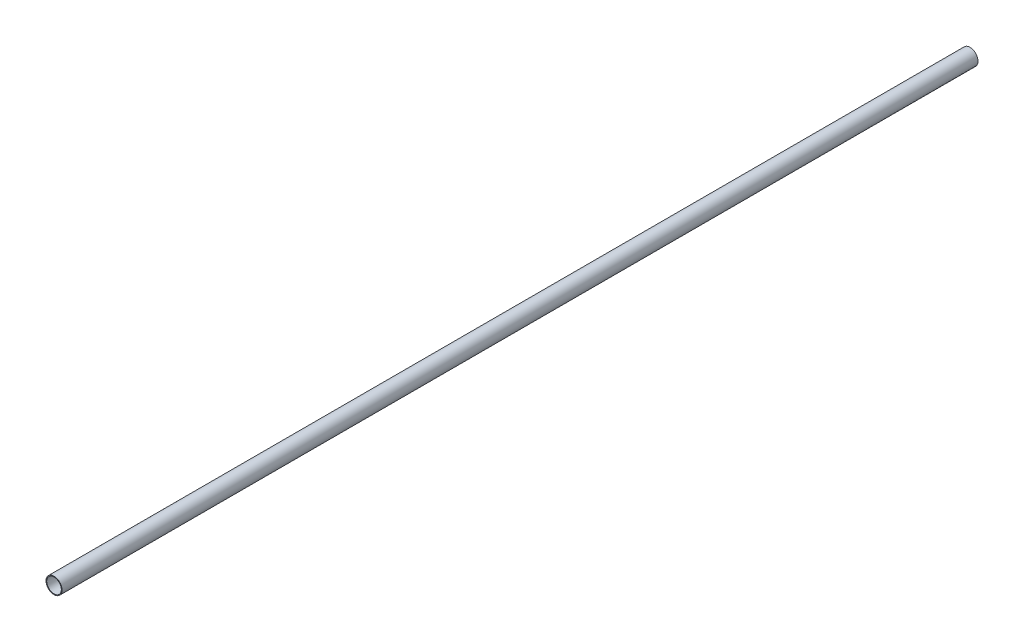
SolidWorks part; units mm, degrees
ref_plane "Front Plane" through (0, 0, 0) normal (0, 0, 1) x (1, 0, 0)
ref_plane "Top Plane" through (0, 0, 0) normal (0, 1, 0) x (1, 0, 0)
ref_plane "Right Plane" through (0, 0, 0) normal (1, 0, 0) x (0, 0, -1)
sketch "Sketch1" plane through (0, 0, 0) normal (0, 0, 1) x (1, 0, 0)
  circle A0 centre (0, 0) radius 2.5
  circle A2 centre (0, 0) radius 2.75
  dimension "D1" = 5
  dimension "D2" = 5.5
extrude "Boss-Extrude3" add sketch "Sketch1" along normal blind 314
